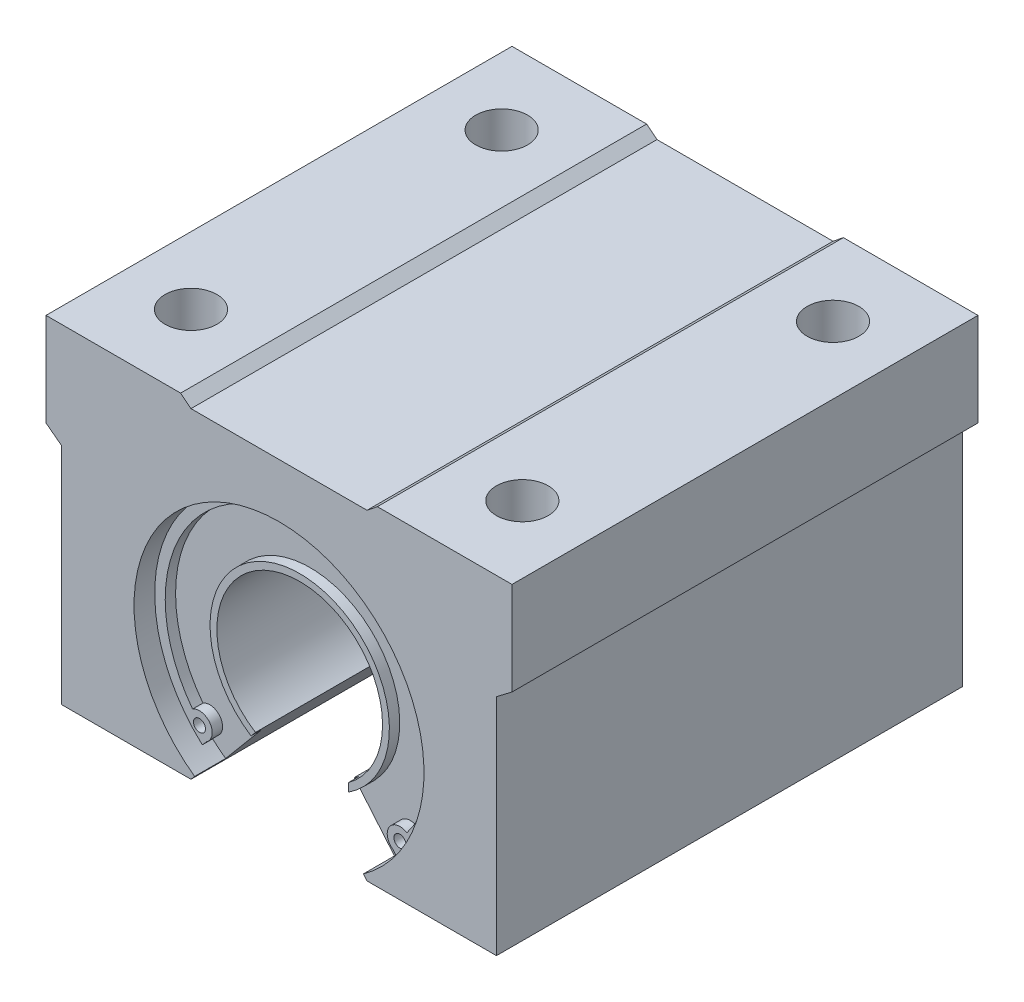
SolidWorks part; units mm, degrees
ref_plane "Plano frontal" through (0, 0, 0) normal (0, 0, 1) x (1, 0, 0)
ref_plane "Plano superior" through (0, 0, 0) normal (0, 1, 0) x (1, 0, 0)
ref_plane "Plano direito" through (0, 0, 0) normal (1, 0, 0) x (0, 0, -1)
sketch "Esboço1" plane through (0, 0, 0) normal (0, 0, 1) x (1, 0, 0)
  line L0 (0, 25.8402) -> (0, -18.843) construction
  line L1 (-25.643, 0) -> (30.31, 0) construction
  line L2 (-22.5, 20) -> (-22.5, 11)
  line L3 (-21, -11.8) -> (-8.5, -11.8)
  line L4 (-22.5, 20) -> (-9.5, 20)
  line L5 (-4.2734, -6.763) -> (-8.5, -11.8)
  line L6 (-21, 9.8641) -> (-21, -11.8)
  line L7 (-9.5, 20) -> (-8.5, 19.2)
  line L8 (8.5, 19.2) -> (-8.5, 19.2)
  line L11 (-22.5, 11) -> (-21, 9.8641)
  line L12 (4.2734, -6.763) -> (8.5, -11.8)
  line L13 (21, -11.8) -> (8.5, -11.8)
  line L14 (21, 9.8641) -> (21, -11.8)
  line L15 (22.5, 11) -> (21, 9.8641)
  line L16 (22.5, 20) -> (22.5, 11)
  line L17 (22.5, 20) -> (9.5, 20)
  line L18 (9.5, 20) -> (8.5, 19.2)
  arc A0 (4.2734, -6.763) -> (-4.2734, -6.763) centre (0, 0) ccw
  point P6 (0, 19.2)
  point P28 (0, 20)
  dimension "D1" = 16
  dimension "D2" = 31.8
  dimension "D3" = 20
  dimension "D4" = 1
  dimension "D5" = 9
  dimension "D6" = 13
  dimension "D7" = 40
  dimension "D8" = 42
  dimension "D9" = 45
  dimension "D10" = 12.5
  dimension "D11" = 31
extrude "Ressalto-extrusão1" add sketch "Esboço1" along normal blind 45
sketch "Esboço3" plane through (0, 0, 0) normal (0, 0, -1) x (-1, 0, 0)
  line L1 (10.5415, 14) -> (-14.5001, 14) construction
  line L5 (9.5, 20) -> (22.5, 20) construction
  circle A0 centre (0, 0) radius 14
  dimension "D1" = 28
  dimension "D2" = 20
extrude "Corte-extrusão2" cut sketch "Esboço3" against normal blind 3
sketch "Esboço4" plane through (0, 0, 3) normal (0, 0, -1) x (-1, 0, 0)
  circle A0 centre (0, 0) radius 8
  circle A1 centre (0, 0) radius 8.6599
extrude "Ressalto-extrusão2" add sketch "Esboço4" along normal blind 1
sketch "Esboço5" plane through (0, 0, 3) normal (0, 0, -1) x (-1, 0, 0)
  line L0 (-8.1502, -11.3831) -> (-4.7012, -7.2728) construction
  line L1 (4.7012, -7.2728) -> (8.1502, -11.3831) construction
  line L2 (-8.1502, -11.3831) -> (-4.7012, -7.2728)
  line L3 (4.7012, -7.2728) -> (8.1502, -11.3831)
  line L4 (-4.7012, -7.2728) -> (-4.7032, -5.655)
  line L5 (4.7012, -7.2728) -> (3.3437, -5.655)
  line L6 (3.3437, -5.655) -> (-4.7032, -5.655)
  line L7 (-8.1502, -11.3831) -> (0.3883, -10.1448)
  line L8 (0.3883, -10.1448) -> (8.1502, -11.3831)
extrude "Corte-extrusão3" cut sketch "Esboço5" along normal blind 1
sketch "Esboço6" plane through (0, 0, 3) normal (0, 0, -1) x (-1, 0, 0)
  line L0 (0, 36.5072) -> (0, -32.3126) construction
  line L1 (-8.9654, -9.8831) -> (-9.8794, -10.8907)
  line L2 (8.9654, -9.8831) -> (9.8794, -10.8907)
  arc A0 (-8.9654, -9.8831) -> (-10.346, -7.8496) centre (-9.6789, -8.8821) ccw
  arc A1 (9.8794, -10.8907) -> (-9.8794, -10.8907) centre (0, 0) ccw
  arc A2 (10.346, -7.8496) -> (-10.346, -7.8496) centre (0, 0) ccw
  circle A3 centre (-9.6789, -8.8821) radius 0.5818
  arc A4 (8.9654, -9.8831) -> (10.346, -7.8496) centre (9.6789, -8.8821) cw
  circle A5 centre (9.6789, -8.8821) radius 0.5818
extrude "Ressalto-extrusão3" add sketch "Esboço6" along normal blind 1
sketch "Esboço7" plane through (0, 0, 3) normal (0, 0, -1) x (-1, 0, 0)
  line L0 (-7.6741, -6.7388) -> (-9.3726, -8.2451) construction
  line L1 (7.7084, -6.7333) -> (9.437, -8.2396) construction
  line L2 (-8.259, -7.2574) -> (-8.7509, -7.6937)
  line L3 (-8.7509, -7.6937) -> (-7.5341, -9.0658)
  line L4 (-7.5341, -9.0658) -> (-6.862, -8.5904)
  line L5 (6.9342, -8.5322) -> (7.5088, -9.1803)
  line L6 (7.5088, -9.1803) -> (8.9995, -7.8583)
  line L7 (8.9995, -7.8583) -> (8.2811, -7.2323)
  arc A2 (-8.259, -7.2574) -> (-6.862, -8.5904) centre (0, 0) ccw
  arc A3 (6.9342, -8.5322) -> (8.2811, -7.2323) centre (0, 0) ccw
ref_plane "Plano1" through (0, 0, 22.5) normal (0, 0, 1) x (1, 0, 0)
sketch "Esboço8" plane through (0, 0, 22.5) normal (0, 0, 1) x (1, 0, 0)
  line L1 (-32.8447, 26.4025) -> (33.8381, 26.4025)
  line L2 (-32.8447, 26.4025) -> (-32.8447, -20.031)
  line L3 (-32.8447, -20.031) -> (33.8381, -20.031)
  line L4 (33.8381, 26.4025) -> (33.8381, -20.031)
extrude "Corte-extrusão5" cut sketch "Esboço8" along normal through all
mirror "Espelhar14" about plane through (0, 0, 22.5) normal (0, 0, 1) of bodies 110
sketch "Esboço9" plane through (0, 20, 0) normal (0, 1, 0) x (1, 0, 0)
  line L0 (-16, -1.567) -> (-16, -46.6155) construction
  line L1 (16, 1.8349) -> (16, -46.0119) construction
  line L2 (0, -46.6155) -> (0, 1.8349) construction
  circle A4 centre (-16, -7.5) radius 2.5
  circle A5 centre (16, -7.5) radius 2.5
  circle A6 centre (16, -37.5) radius 2.5
  circle A7 centre (-16, -37.5) radius 2.5
  dimension "D1" = 5
  dimension "D2" = 5
  dimension "D3" = 5
  dimension "D4" = 5
  dimension "D5" = 16
extrude "Corte-extrusão6" cut sketch "Esboço9" against normal blind 14
